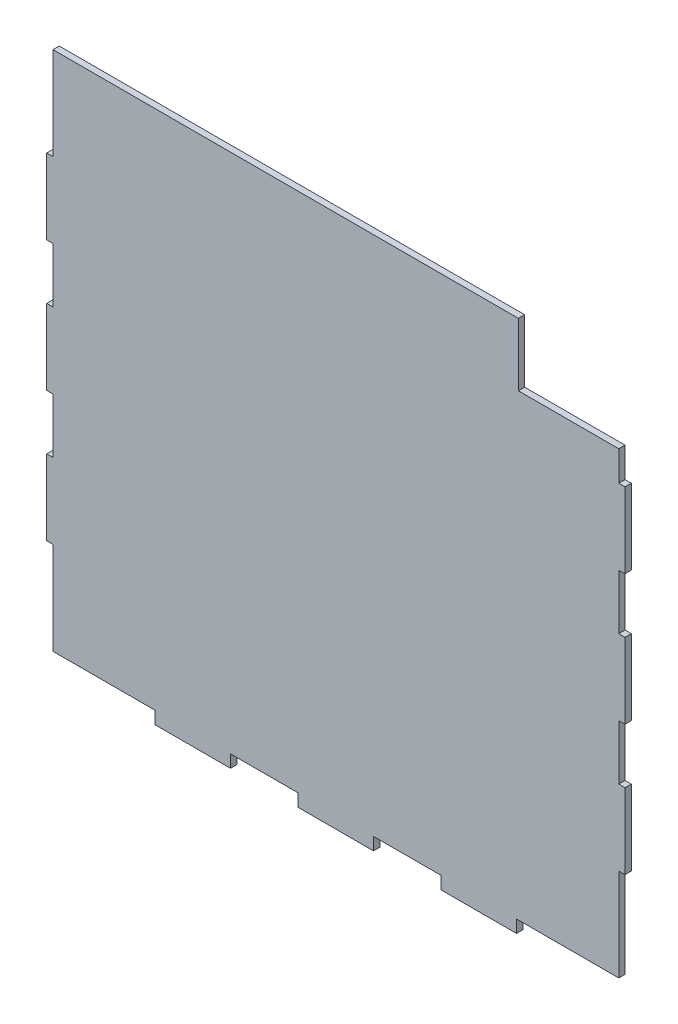
SolidWorks part; units mm, degrees
ref_plane "Front" through (0, 0, 0) normal (0, 0, 1) x (1, 0, 0)
ref_plane "Top" through (0, 0, 0) normal (0, 1, 0) x (1, 0, 0)
ref_plane "Right" through (0, 0, 0) normal (1, 0, 0) x (0, 0, -1)
sketch "Sketch1" plane through (0, 0, 0) normal (0, 0, 1) x (1, 0, 0)
  line L0 (0, 266.85) -> (0, 0) construction
  line L1 (0, 0) -> (-289.475, 0) construction
  line L2 (-289.475, 0) -> (-289.475, 266.85) construction
  line L3 (0, 266.85) -> (-289.475, 266.85) construction
  line L4 (0, 266.85) -> (0, 0) construction
  line L5 (0, 0) -> (-289.475, 0) construction
  line L6 (-289.475, 0) -> (-289.475, 266.85) construction
  line L7 (0, 266.85) -> (-289.475, 266.85) construction
  line L9 (-287.8875, 266.85) -> (-1.5875, 266.85)
  line L11 (-287.8875, 3.175) -> (-1.5875, 3.175)
  line L38 (-287.8875, 3.175) -> (-287.8875, 266.85)
  line L39 (-1.5875, 266.85) -> (-1.5875, 3.175)
  point P4 (-72.3688, 0)
  point P6 (-144.7375, 0)
  point P8 (0, 69.0937)
  point P10 (0, 135.0125)
  point P12 (0, 200.9312)
  point P14 (-289.475, 69.0937)
  point P16 (-289.475, 135.0125)
  point P18 (-289.475, 200.9312)
  point P20 (-217.1063, 0)
  dimension "D2" = 3.175
  dimension "D1" = 1.5875
  dimension "D3" = 1.5875
extrude "Boss-Extrude1" add sketch "Sketch1" along normal mid plane 3.175
sketch "Sketch4" plane through (0, 0, 1.5875) normal (0, 0, 1) x (1, 0, 0)
  line L0 (-287.8875, 3.175) -> (-287.8875, 266.85) construction
  line L1 (-291.0625, 181.8812) -> (-287.8875, 181.8812)
  line L2 (-291.0625, 181.8812) -> (-291.0625, 219.9812)
  line L3 (-291.0625, 219.9812) -> (-287.8875, 219.9812)
  line L4 (-287.8875, 181.8812) -> (-287.8875, 219.9812)
  line L5 (-291.0625, 181.8812) -> (-287.8875, 219.9812) construction
  line L6 (-291.0625, 219.9812) -> (-287.8875, 181.8812) construction
  line L7 (-1.5875, 266.85) -> (-1.5875, 3.175) construction
  line L8 (-291.0625, 115.9625) -> (-287.8875, 115.9625)
  line L9 (-291.0625, 115.9625) -> (-291.0625, 154.0625)
  line L10 (-291.0625, 154.0625) -> (-287.8875, 154.0625)
  line L11 (-287.8875, 115.9625) -> (-287.8875, 154.0625)
  line L12 (-291.0625, 115.9625) -> (-287.8875, 154.0625) construction
  line L13 (-291.0625, 154.0625) -> (-287.8875, 115.9625) construction
  line L14 (-291.0625, 50.0437) -> (-287.8875, 50.0437)
  line L15 (-291.0625, 50.0437) -> (-291.0625, 88.1437)
  line L16 (-291.0625, 88.1437) -> (-287.8875, 88.1437)
  line L17 (-287.8875, 50.0437) -> (-287.8875, 88.1437)
  line L18 (-291.0625, 50.0437) -> (-287.8875, 88.1437) construction
  line L19 (-291.0625, 88.1437) -> (-287.8875, 50.0437) construction
  line L20 (1.5875, 181.8812) -> (-1.5875, 181.8812)
  line L21 (1.5875, 181.8812) -> (1.5875, 219.9812)
  line L22 (1.5875, 219.9812) -> (-1.5875, 219.9812)
  line L23 (-1.5875, 181.8812) -> (-1.5875, 219.9812)
  line L24 (1.5875, 181.8812) -> (-1.5875, 219.9812) construction
  line L25 (1.5875, 219.9812) -> (-1.5875, 181.8812) construction
  line L26 (-287.8875, 3.175) -> (-1.5875, 3.175) construction
  line L27 (1.5875, 115.9625) -> (-1.5875, 115.9625)
  line L28 (1.5875, 115.9625) -> (1.5875, 154.0625)
  line L29 (1.5875, 154.0625) -> (-1.5875, 154.0625)
  line L30 (-1.5875, 115.9625) -> (-1.5875, 154.0625)
  line L31 (1.5875, 115.9625) -> (-1.5875, 154.0625) construction
  line L32 (1.5875, 154.0625) -> (-1.5875, 115.9625) construction
  line L33 (1.5875, 50.0437) -> (-1.5875, 50.0437)
  line L34 (1.5875, 50.0437) -> (1.5875, 88.1437)
  line L35 (1.5875, 88.1437) -> (-1.5875, 88.1437)
  line L36 (-1.5875, 50.0437) -> (-1.5875, 88.1437)
  line L37 (1.5875, 50.0437) -> (-1.5875, 88.1437) construction
  line L38 (1.5875, 88.1437) -> (-1.5875, 50.0437) construction
  line L39 (-236.1563, -3.175) -> (-198.0563, -3.175)
  line L40 (-236.1563, -3.175) -> (-236.1563, 3.175)
  line L41 (-236.1563, 3.175) -> (-198.0563, 3.175)
  line L42 (-198.0563, -3.175) -> (-198.0563, 3.175)
  line L43 (-236.1563, -3.175) -> (-198.0563, 3.175) construction
  line L44 (-236.1563, 3.175) -> (-198.0563, -3.175) construction
  line L45 (0, 0) -> (-289.475, 0) construction
  line L46 (-163.7875, -3.175) -> (-125.6875, -3.175)
  line L47 (-163.7875, -3.175) -> (-163.7875, 3.175)
  line L48 (-163.7875, 3.175) -> (-125.6875, 3.175)
  line L49 (-125.6875, -3.175) -> (-125.6875, 3.175)
  line L50 (-163.7875, -3.175) -> (-125.6875, 3.175) construction
  line L51 (-163.7875, 3.175) -> (-125.6875, -3.175) construction
  line L53 (-91.4188, -3.175) -> (-53.3188, -3.175)
  line L54 (-91.4188, -3.175) -> (-91.4188, 3.175)
  line L55 (-91.4188, 3.175) -> (-53.3188, 3.175)
  line L56 (-53.3188, -3.175) -> (-53.3188, 3.175)
  line L57 (-91.4188, -3.175) -> (-53.3188, 3.175) construction
  line L58 (-91.4188, 3.175) -> (-53.3188, -3.175) construction
  point P0 (-289.475, 200.9312)
  point P8 (-289.475, 135.0125)
  point P14 (-289.475, 69.0937)
  point P20 (0, 200.9312)
  point P28 (0, 135.0125)
  point P34 (0, 69.0937)
  point P40 (-217.1063, 0)
  point P49 (-144.7375, 0)
  point P56 (-72.3688, 0)
  dimension "D1" = 38.1
extrude "Boss-Extrude2" add sketch "Sketch4" against normal up to surface (3.175 mm away) up to face at (-144.7375, 135.0125, -1.5875)
sketch "Sketch5" plane through (0, 0, 1.5875) normal (0, 0, 1) x (1, 0, 0)
  line L0 (-289.475, 200.9312) -> (-289.01, 221.1038) construction
  line L2 (-289.01, 221.1038) -> (-289.01, 219.9812) construction
  line L4 (-287.8875, 219.9812) -> (-291.0625, 219.9812) construction
  line L6 (-289.01, 221.1038) -> (-287.8875, 221.1038) construction
  line L7 (-287.8875, 3.175) -> (-287.8875, 266.85) construction
  line L8 (-289.01, 221.1038) -> (-287.8875, 219.9812) construction
  line L10 (-287.8875, 200.9313) -> (-291.0625, 200.9312) construction
  line L11 (-291.0625, 219.9812) -> (-291.0625, 181.8812) construction
  line L12 (-289.475, 200.9312) -> (-289.01, 180.7587) construction
  line L14 (-289.475, 135.0125) -> (-289.01, 155.185) construction
  line L15 (-289.475, 135.0125) -> (-289.01, 114.84) construction
  line L17 (-289.475, 69.0937) -> (-289.01, 89.2663) construction
  line L19 (-289.475, 69.0937) -> (-289.01, 48.9212) construction
  line L20 (0, 200.9312) -> (-0.5099, 221.0589) construction
  line L24 (-0.5099, 221.0589) -> (-0.5099, 219.9812) construction
  line L26 (1.5875, 219.9812) -> (-1.5875, 219.9812) construction
  line L28 (-0.5099, 221.0589) -> (-1.5875, 221.0589) construction
  line L29 (-1.5875, 266.85) -> (-1.5875, 3.175) construction
  line L30 (-0.5099, 221.0589) -> (-1.5875, 219.9812) construction
  line L32 (-1.5875, 200.9312) -> (1.5875, 200.9313) construction
  line L34 (1.5875, 181.8812) -> (1.5875, 219.9812) construction
  line L35 (0, 200.9312) -> (-0.5099, 180.8036) construction
  line L36 (0, 135.0125) -> (-0.5099, 114.8849) construction
  line L38 (0, 135.0125) -> (-0.5099, 155.1401) construction
  line L40 (0, 69.0937) -> (-0.5099, 48.9661) construction
  line L41 (0, 69.0937) -> (-0.5099, 89.2214) construction
  line L45 (-217.1063, 0) -> (-237.2788, 2.0525) construction
  line L47 (-237.2788, 2.0525) -> (-236.1563, 2.0525) construction
  line L48 (-236.1563, 3.175) -> (-236.1563, -3.175) construction
  line L49 (-237.2788, 2.0525) -> (-237.2788, 3.175) construction
  line L51 (-287.8875, 3.175) -> (-1.5875, 3.175) construction
  line L53 (-237.2788, 2.0525) -> (-236.1563, 3.175) construction
  line L54 (-217.1063, 3.175) -> (-217.1063, -3.175) construction
  line L55 (-236.1563, -3.175) -> (-198.0563, -3.175) construction
  line L57 (-217.1063, 0) -> (-196.9337, 2.0525) construction
  line L59 (-144.7375, 0) -> (-164.91, 2.0525) construction
  line L60 (-144.7375, 0) -> (-124.565, 2.0525) construction
  line L61 (-72.3688, 0) -> (-92.5413, 2.0525) construction
  line L62 (-72.3688, 0) -> (-52.1962, 2.0525) construction
  circle A18 centre (-289.01, 221.1038) radius 1.5875
  circle A19 centre (-289.01, 180.7587) radius 1.5875
  circle A20 centre (-289.01, 155.185) radius 1.5875
  circle A21 centre (-289.01, 114.84) radius 1.5875
  circle A22 centre (-289.01, 89.2663) radius 1.5875
  circle A23 centre (-289.01, 48.9212) radius 1.5875
  circle A24 centre (-0.5099, 221.0589) radius 1.524
  circle A25 centre (-0.5099, 180.8036) radius 1.524
  circle A26 centre (-0.5099, 155.1401) radius 1.524
  circle A27 centre (-0.5099, 114.8849) radius 1.524
  circle A28 centre (-0.5099, 89.2214) radius 1.524
  circle A29 centre (-0.5099, 48.9661) radius 1.524
  circle A30 centre (-237.2788, 2.0525) radius 1.5875
  circle A31 centre (-196.9337, 2.0525) radius 1.5875
  circle A32 centre (-124.565, 2.0525) radius 1.5875
  circle A33 centre (-164.91, 2.0525) radius 1.5875
  circle A34 centre (-52.1962, 2.0525) radius 1.5875
  circle A35 centre (-92.5413, 2.0525) radius 1.5875
  point P15 (-289.475, 200.9312)
  point P41 (0, 200.9312)
  point P69 (-217.1063, 0)
  dimension "D1" = 1.5875
  dimension "D3" = 45
  dimension "D4" = 1.524
  dimension "D5" = 45
  dimension "D7" = 1.5875
  dimension "D8" = 45
  dimension "D2" = 3
  dimension "D6" = 3
sketch "Sketch2" plane through (0, 0, 1.5875) normal (0, 0, 1) x (1, 0, 0)
  line L0 (-1.5875, 266.85) -> (-287.8875, 266.85) construction
  line L1 (-287.8875, 266.85) -> (-237.0875, 266.85)
  line L2 (-287.8875, 266.85) -> (-287.8875, 235.1)
  line L3 (-287.8875, 235.1) -> (-237.0875, 235.1)
  line L4 (-237.0875, 266.85) -> (-237.0875, 235.1)
  dimension "D2" = 50.8
extrude "Cut-Extrude1" [suppressed] cut sketch "Sketch2" against normal up to surface (3.175 mm away)
sketch "Sketch3" plane through (0, 0, 1.5875) normal (0, 0, 1) x (1, 0, 0)
  line L0 (-1.5875, 266.85) -> (-287.8875, 266.85) construction
  line L1 (-1.5875, 266.85) -> (-52.3875, 266.85)
  line L2 (-1.5875, 266.85) -> (-1.5875, 235.1)
  line L3 (-1.5875, 235.1) -> (-52.3875, 235.1)
  line L4 (-52.3875, 266.85) -> (-52.3875, 235.1)
extrude "Cut-Extrude2" cut sketch "Sketch3" against normal up to surface (3.175 mm away)
extrude "Cut-Extrude4" [suppressed] cut sketch "Sketch5" against normal up to surface (3.175 mm away)
equation "\"D2@Sketch1\"=\"acc bottom wall thickness@FS2-EN-ACC-A-0003-V1, ACCUMULATOR CONTAINER-1.Assembly\"/2"
equation "\"D1@Sketch2\"=\"acc side wall extra height@FS2-EN-ACC-A-0003-V1, ACCUMULATOR CONTAINER-1.Assembly\""
equation "\"D1@Sketch3\"=\"acc side wall extra height@FS2-EN-ACC-A-0003-V1, ACCUMULATOR CONTAINER-1.Assembly\""
equation "\"D1@Sketch4\"=\"weld slot length@FS2-EN-ACC-A-0003-V1, ACCUMULATOR CONTAINER-1.Assembly\""
equation "\"D1@Sketch5\"=\"weld teardrop radius@FS2-EN-ACC-A-0003-V1, ACCUMULATOR CONTAINER-1.Assembly\""
equation "\"D7@Sketch5\"=\"weld teardrop radius@FS2-EN-ACC-A-0003-V1, ACCUMULATOR CONTAINER-1.Assembly\""
